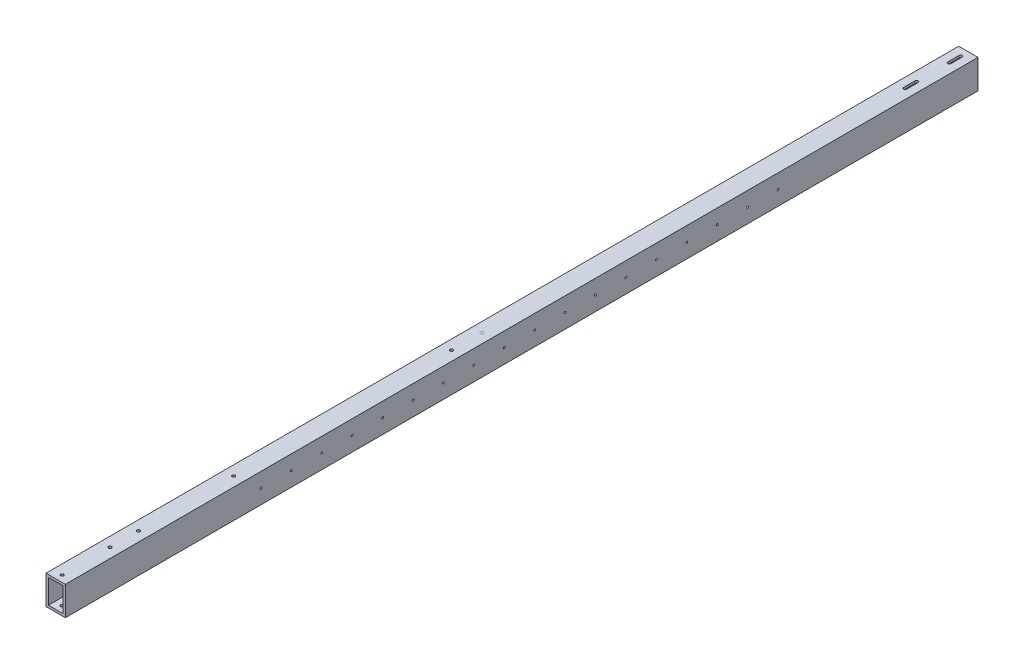
SolidWorks part; units mm, degrees
material "1.0545 (S355N)"
ref_plane "Front Plane" through (0, 0, 0) normal (0, 0, 1) x (1, 0, 0)
ref_plane "Top Plane" through (0, 0, 0) normal (0, 1, 0) x (1, 0, 0)
ref_plane "Right Plane" through (0, 0, 0) normal (1, 0, 0) x (0, 0, -1)
sketch "Sketch1" plane through (0, 0, 0) normal (0, 0, 1) x (1, 0, 0)
  line L0 (19.05, 31.75) -> (-19.05, 31.75)
  line L1 (25.4, 38.1) -> (-25.4, 38.1)
  line L2 (25.4, 38.1) -> (25.4, -38.1)
  line L3 (25.4, -38.1) -> (-25.4, -38.1)
  line L4 (-25.4, 38.1) -> (-25.4, -38.1)
  line L5 (25.4, 38.1) -> (-25.4, -38.1) construction
  line L6 (25.4, -38.1) -> (-25.4, 38.1) construction
  line L7 (-19.05, 31.75) -> (-19.05, -31.75)
  line L8 (19.05, -31.75) -> (-19.05, -31.75)
  line L9 (19.05, 31.75) -> (19.05, -31.75)
  point P0 (0, 0)
  dimension "D1" = 50.8
  dimension "D2" = 76.2
  dimension "D3" = 6.35
extrude "Boss-Extrude1" add sketch "Sketch1" along normal blind 2400
sketch "Sketch2" plane through (0, 38.1, 0) normal (0, 1, 0) x (1, 0, 0)
  line L2 (0, -136) -> (0, -166) construction
  line L3 (4, -136) -> (4, -166)
  line L4 (-4, -136) -> (-4, -166)
  line L5 (0, -20) -> (0, -50) construction
  line L6 (3.9978, -20) -> (3.9978, -50)
  line L7 (-3.9978, -20) -> (-3.9978, -50)
  line L9 (25.4, -2400) -> (-25.4, -2400) construction
  arc A2 (4, -136) -> (-4, -136) centre (0, -136) ccw
  arc A3 (-4, -166) -> (4, -166) centre (0, -166) ccw
  arc A4 (3.9978, -20) -> (-3.9978, -20) centre (0, -20) ccw
  circle A5 centre (0, -2383) radius 4
  circle A7 centre (0, -2257) radius 4
  arc A9 (-3.9978, -50) -> (3.9978, -50) centre (0, -50) ccw
  point P3 (0, -35)
  point P4 (0, -151)
  point P20 (0, -2400)
  dimension "D3" = 30
  dimension "D4" = 4
  dimension "D5" = 30
  dimension "D8" = 3.9978
  dimension "D6" = 8
  dimension "D9" = 8
  dimension "D1" = 116
  dimension "D2" = 20
  dimension "D7" = 17
  dimension "D14" = 126
ref_plane "Plane1" through (0, 0, 1279) normal (0, 0, 1) x (1, 0, 0)
extrude "Cut-Extrude1" cut sketch "Sketch2" against normal through all contours A5
sketch "Sketch3" plane through (25.4, 0, 0) normal (1, 0, 0) x (0, 0, -1)
  line L0 (-2400, -38.1) -> (-2400, 38.1) construction
  circle A0 centre (-1885.8, 0) radius 2.5
  circle A1 centre (-1805.8, 0) radius 2.5
  circle A2 centre (-1725.8, 0) radius 2.5
  circle A3 centre (-1645.8, 0) radius 2.5
  circle A4 centre (-1565.8, 0) radius 2.5
  circle A5 centre (-1485.8, 0) radius 2.5
  circle A6 centre (-1405.8, 0) radius 2.5
  circle A7 centre (-1325.8, 0) radius 2.5
  circle A8 centre (-1245.8, 0) radius 2.5
  circle A9 centre (-1165.8, 0) radius 2.5
  circle A10 centre (-1085.8, 0) radius 2.5
  circle A11 centre (-1005.8, 0) radius 2.5
  circle A12 centre (-925.8, 0) radius 2.5
  circle A13 centre (-845.8, 0) radius 2.5
  circle A14 centre (-765.8, 0) radius 2.5
  circle A15 centre (-685.8, 0) radius 2.5
  circle A16 centre (-605.8, 0) radius 2.5
  circle A17 centre (-525.8, 0) radius 2.5
  point P6 (-2400, 0)
  dimension "D1" = 5
  dimension "D4" = 80
  dimension "D2" = 514.2
  dimension "D3" = 18
extrude "Cut-Extrude2" cut sketch "Sketch3" against normal blind 2438.4
sketch "Sketch4" plane through (0, 38.1, 0) normal (0, 1, 0) x (1, 0, 0)
  circle A0 centre (0, -2182) radius 3.95 construction
  circle A1 centre (0, -1932) radius 3.95 construction
  circle A2 centre (0, -2182) radius 3.95
  circle A3 centre (0, -1932) radius 3.95
extrude "Cut-Extrude3" cut sketch "Sketch4" against normal through all
sketch "Sketch5" plane through (0, 38.1, 0) normal (0, 1, 0) x (1, 0, 0)
  line L2 (-109.6, -1300.1) -> (-99.6, -1300.1)
  line L3 (-99.6, -1289.1) -> (-109.6, -1289.1)
  line L4 (-109.6, -1300.1) -> (-99.6, -1300.1)
  line L5 (-99.6, -1289.1) -> (-109.6, -1289.1)
  circle A0 centre (0, -1279) radius 3.95 construction
  circle A1 centre (0, -1279) radius 3.95
  circle A3 centre (0, -1359) radius 4
  circle A4 centre (0, -1359) radius 4
  circle A5 centre (0, -1279) radius 4
  circle A6 centre (0, -1279) radius 4
  arc A8 (-99.6, -1300.1) -> (-99.6, -1289.1) centre (-99.6, -1294.6) ccw
  arc A9 (-109.6, -1289.1) -> (-109.6, -1300.1) centre (-109.6, -1294.6) ccw
  arc A10 (-99.6, -1300.1) -> (-99.6, -1289.1) centre (-99.6, -1294.6) ccw
  arc A11 (-109.6, -1289.1) -> (-109.6, -1300.1) centre (-109.6, -1294.6) ccw
  dimension "D1" = 0
  dimension "D2" = 0
  dimension "D3" = 0
extrude "Cut-Extrude4" cut sketch "Sketch5" against normal through all
